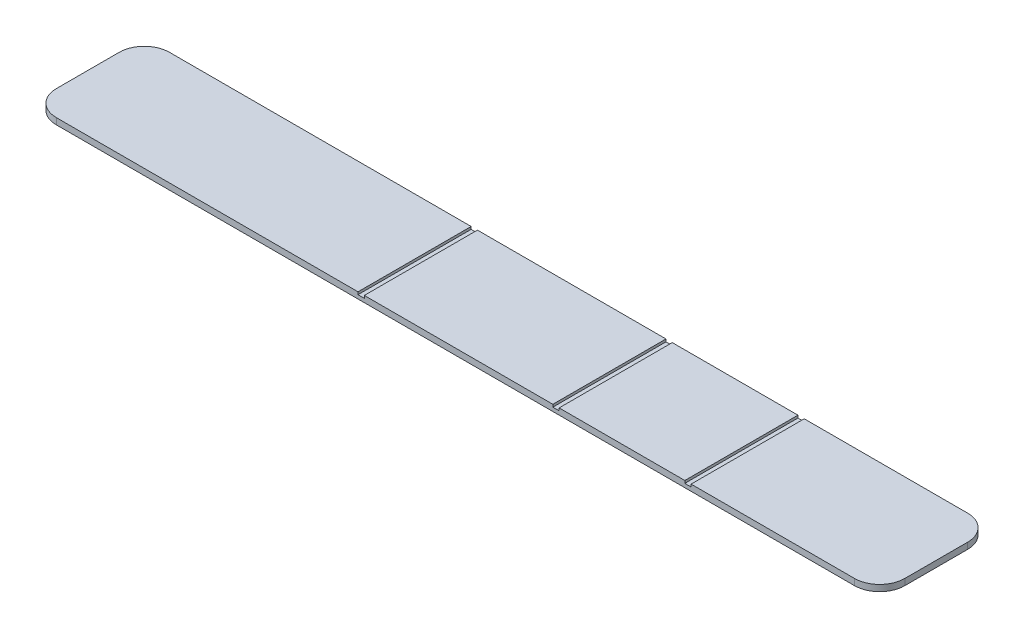
SolidWorks part; units mm, degrees
ref_plane "Front Plane" through (0, 0, 0) normal (0, 0, 1) x (1, 0, 0)
ref_plane "Top Plane" through (0, 0, 0) normal (0, 1, 0) x (1, 0, 0)
ref_plane "Right Plane" through (0, 0, 0) normal (1, 0, 0) x (0, 0, -1)
sketch "Sketch1" plane through (0, 0, 0) normal (0, 1, 0) x (1, 0, 0)
  line L1 (0, 0) -> (135, 0)
  line L2 (0, 0) -> (0, 18)
  line L3 (0, 18) -> (135, 18)
  line L4 (135, 0) -> (135, 18)
  dimension "D1" = 18
  dimension "D2" = 135
extrude "Boss-Extrude1" add sketch "Sketch1" along normal blind 1 contours L1 L4 L3 L2
sketch "Sketch2" plane through (0, 1, 0) normal (0, 1, 0) x (1, 0, 0)
  line L0 (0, 18) -> (135, 18) construction
  line L1 (52, 18) -> (53, 18)
  line L2 (52, 18) -> (52, 0)
  line L3 (52, 0) -> (53, 0)
  line L4 (53, 18) -> (53, 0)
  line L5 (0, 0) -> (135, 0) construction
  line L6 (0, 0) -> (0, 18) construction
  line L7 (83, 18) -> (84, 18)
  line L8 (83, 18) -> (83, 0)
  line L9 (83, 0) -> (84, 0)
  line L10 (84, 18) -> (84, 0)
  line L11 (104, 18) -> (105, 18)
  line L12 (104, 18) -> (104, 0)
  line L13 (104, 0) -> (105, 0)
  line L14 (105, 18) -> (105, 0)
  dimension "D1" = 1
  dimension "D2" = 1
  dimension "D3" = 1
  dimension "D4" = 30
  dimension "D5" = 20
  dimension "D6" = 52
extrude "Cut-Extrude1" cut sketch "Sketch2" against normal blind 0.4
fillet "Fillet1" radius 4 4 edges at (135, 0.5, -18) (135, 0.5, 0) (0, 0.5, -18) (0, 0.5, 0)
